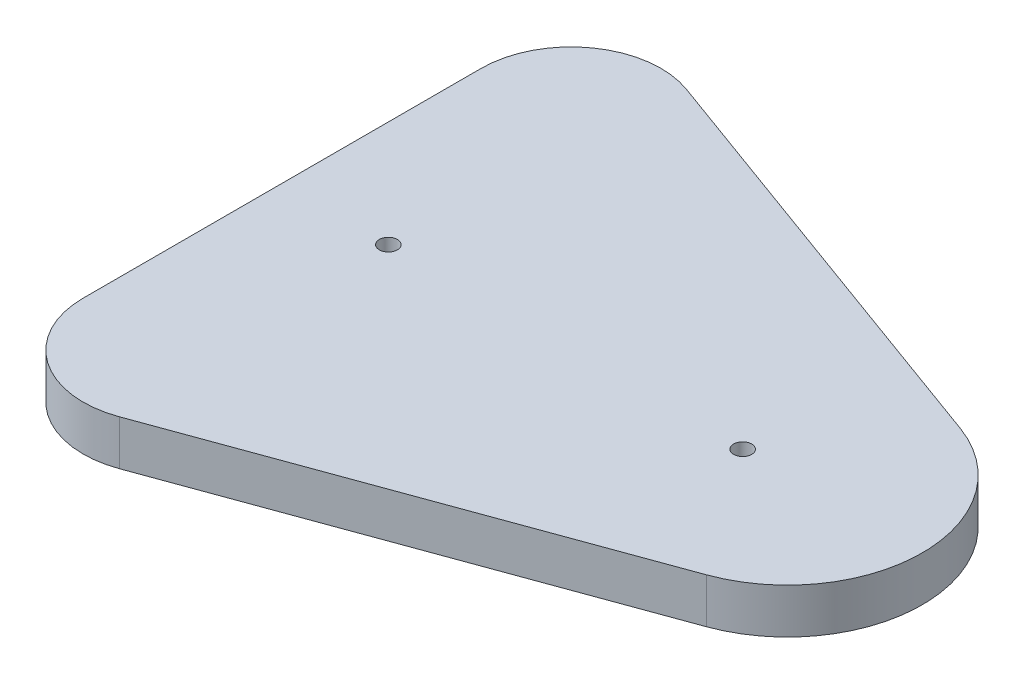
SolidWorks part; units mm, degrees
ref_plane "Front Plane" through (0, 0, 0) normal (0, 0, 1) x (1, 0, 0)
ref_plane "Top Plane" through (0, 0, 0) normal (0, 1, 0) x (1, 0, 0)
ref_plane "Right Plane" through (0, 0, 0) normal (1, 0, 0) x (0, 0, -1)
sketch "Sketch1" plane through (0, 0, 0) normal (0, 1, 0) x (1, 0, 0)
  line L0 (8.6876, -23.8681) -> (130.2345, 20.3729)
  line L1 (130.2345, 91.9771) -> (8.6876, 136.2181)
  line L2 (-25.4, 112.35) -> (-25.4, 0)
  arc A0 (-25.4, 0) -> (8.6876, -23.8681) centre (0, 0) ccw
  arc A1 (8.6876, 136.2181) -> (-25.4, 112.35) centre (0, 112.35) ccw
  arc A2 (130.2345, 20.3729) -> (130.2345, 91.9771) centre (117.2031, 56.175) ccw
  point P1 (-208.6209, 70.501)
  point P7 (-403.3058, -72.6805)
  dimension "D1" = 112.35
  dimension "D2" = 129.97
  dimension "D3" = 129.97
extrude "Boss-Extrude1" add sketch "Sketch1" along normal blind 12.7
hole_wizard "1/4-20 Tapped Hole1" positions "3DSketch3" profile "Sketch4" tap size "1/4-20" standard "ANSI Inch"
sketch3d "3DSketch3"
  line L0 (-25.4, 12.7, -112.35) -> (-25.4, 12.7, 0) construction
  point P0 (4.6, 12.7, -56.175)
  point P2 (104.6, 12.7, -56.175)
  dimension "D1" = 100
  dimension "D2" = 30
sketch "Sketch4" plane through (4.6, 12.7, -56.175) normal (1, 0, 0) x (0, 0, 1)
  line L0 (0, 0) -> (0, 20.5838)
  line L1 (0, 20.5838) -> (2.5527, 19.05)
  line L2 (2.5527, 19.05) -> (2.5527, 0)
  line L5 (2.5527, 0) -> (0, 0)
  line L10 (0, 20.5838) -> (-2.5527, 19.05) construction
  line L11 (0, -6.35) -> (0, 107.95) construction
  dimension "Tap Drill Dia." = 5.1054
  dimension "Tap Drill Depth" = 19.05
  dimension "Drill Angle" = 118
cosmetic thread "Hole Thread1" parameters "D1"=12.7, "D2"=6.35
cosmetic thread "Hole Thread2" parameters "D1"=12.7, "D2"=6.35
